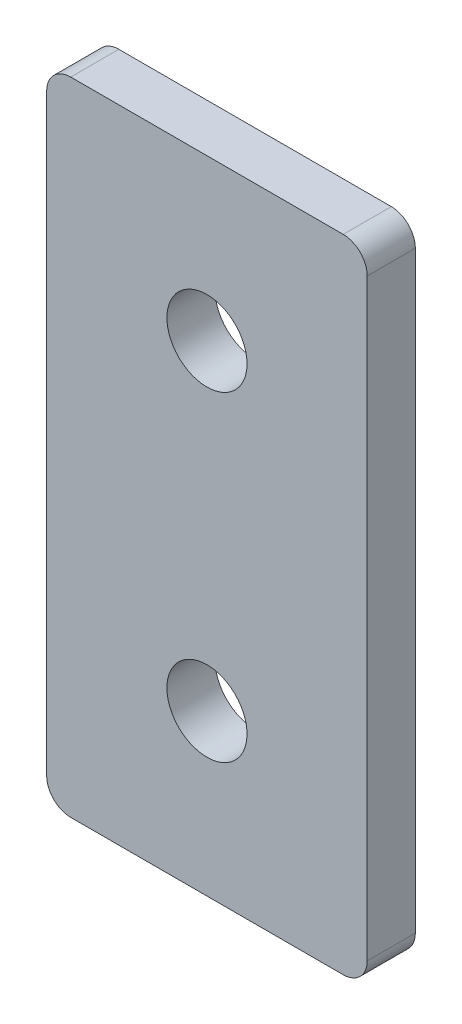
SolidWorks part; units mm, degrees
ref_plane "Front" through (0, 0, 0) normal (0, 0, 1) x (1, 0, 0)
ref_plane "Top" through (0, 0, 0) normal (0, 1, 0) x (1, 0, 0)
ref_plane "Right" through (0, 0, 0) normal (1, 0, 0) x (0, 0, -1)
sketch "Model" plane through (0, 0, 0) normal (0, 0, 1) x (1, 0, 0)
  line L0 (8.5, 0) -> (-8.5, 0)
  line L1 (-10, 1.5) -> (-10, 38.5)
  line L2 (10, 38.5) -> (10, 1.5)
  line L3 (-8.5, 40) -> (8.5, 40)
  line L4 (0, 0) -> (0, 40) construction
  line L5 (10, 20) -> (-10, 20) construction
  circle A0 centre (0, 30) radius 2.5
  circle A1 centre (0, 10) radius 2.5
  arc A2 (-10, 1.5) -> (-8.5, 0) centre (-8.5, 1.5) ccw
  arc A3 (-8.5, 40) -> (-10, 38.5) centre (-8.5, 38.5) ccw
  arc A4 (10, 38.5) -> (8.5, 40) centre (8.5, 38.5) ccw
  arc A5 (8.5, 0) -> (10, 1.5) centre (8.5, 1.5) ccw
  dimension "D1" = 5
  dimension "D5" = 1.5
  dimension "D2" = 40
  dimension "D3" = 20
  dimension "D4" = 20
extrude "Boss-Extrude1" add sketch "Model" along normal blind 3
